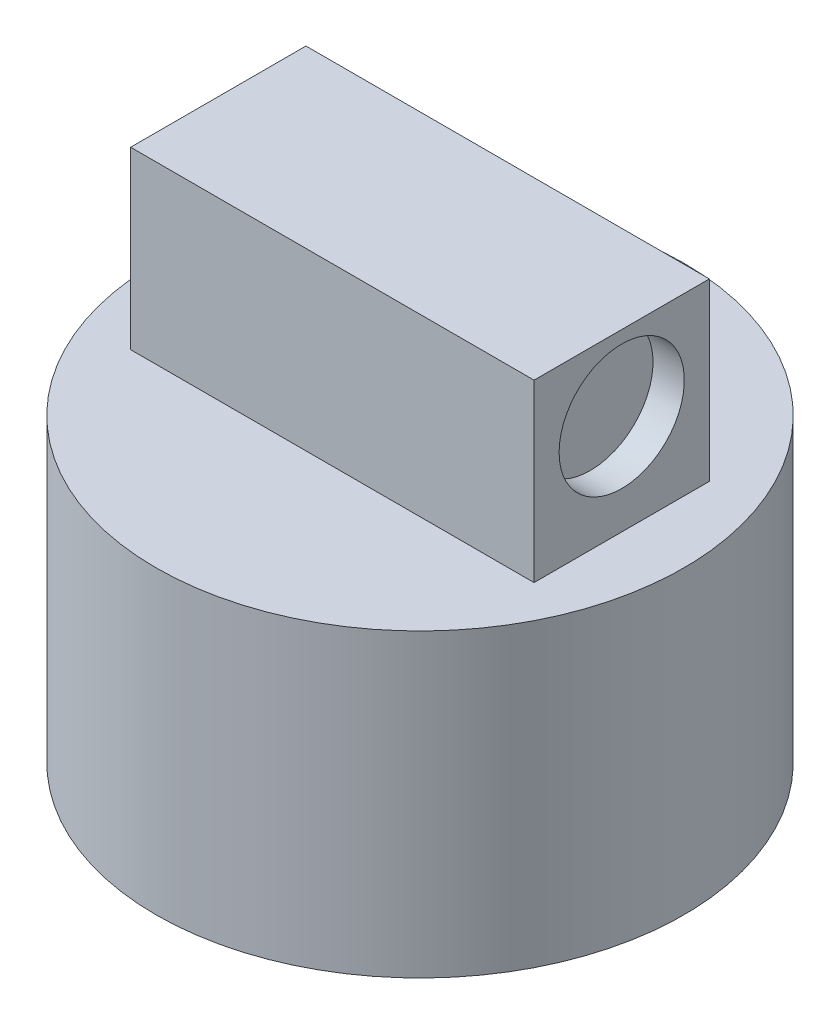
SolidWorks part; units mm, degrees
ref_plane "Front Plane" through (0, 0, 0) normal (0, 0, 1) x (1, 0, 0)
ref_plane "Top Plane" through (0, 0, 0) normal (0, 1, 0) x (1, 0, 0)
ref_plane "Right Plane" through (0, 0, 0) normal (1, 0, 0) x (0, 0, -1)
sketch "Sketch1" plane through (0, 0, 0) normal (0, 1, 0) x (1, 0, 0)
  circle A0 centre (0, 5.9514) radius 42.15
  dimension "D1" = 84.3
extrude "Boss-Extrude1" add sketch "Sketch1" along normal blind 48
sketch "Sketch2" plane through (0, 48, 0) normal (0, 1, 0) x (1, 0, 0)
  line L1 (32.215, -8.0486) -> (-32.215, -8.0486)
  line L2 (32.215, -8.0486) -> (32.215, 19.9514)
  line L3 (32.215, 19.9514) -> (-32.215, 19.9514)
  line L4 (-32.215, -8.0486) -> (-32.215, 19.9514)
  line L5 (32.215, -8.0486) -> (-32.215, 19.9514) construction
  line L6 (32.215, 19.9514) -> (-32.215, -8.0486) construction
  point P0 (0, 5.9514)
  dimension "D1" = 64.43
  dimension "D2" = 28
extrude "Boss-Extrude2" add sketch "Sketch2" along normal blind 28
sketch "Sketch3" plane through (-32.215, 0, 0) normal (-1, 0, 0) x (0, 0, 1)
  line L0 (-5.9514, 48) -> (-5.9514, 64)
  line L1 (-19.9514, 48) -> (8.0486, 48) construction
  circle A0 centre (-5.9514, 64) radius 10
  dimension "D1" = 16
extrude "Cut-Extrude1" cut sketch "Sketch3" against normal blind 5
ref_plane "Plane1" through (0, 0, 0) normal (-1, 0, 0) x (0, 0, 1)
mirror "Mirror2" about plane through (0, 0, 0) normal (-1, 0, 0) of "Cut-Extrude1"
